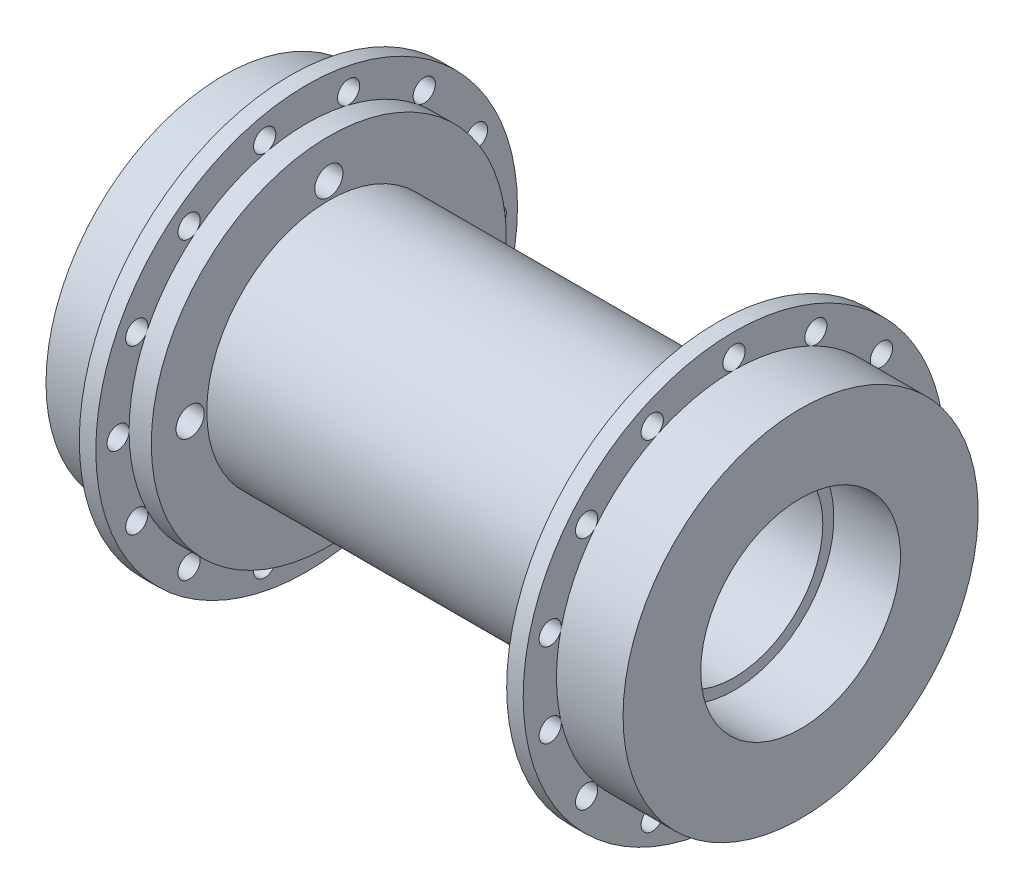
SolidWorks part; units mm, degrees
ref_plane "Front" through (0, 0, 0) normal (0, 0, 1) x (1, 0, 0)
ref_plane "Top" through (0, 0, 0) normal (0, 1, 0) x (1, 0, 0)
ref_plane "Right" through (0, 0, 0) normal (1, 0, 0) x (0, 0, -1)
sketch "Sketch1" plane through (0, 0, 0) normal (0, 0, 1) x (1, 0, 0)
  line L0 (-48.6984, 0) -> (52.2764, 0) construction
  line L1 (41.275, 25.4) -> (41.275, 14.2875)
  line L2 (41.275, 25.4) -> (31.75, 25.4)
  line L3 (31.75, 25.4) -> (31.75, 30.1625)
  line L4 (31.75, 30.1625) -> (29.3878, 30.1625)
  line L5 (29.3878, 30.1625) -> (29.3878, 25.4)
  line L6 (26.2128, 17.4625) -> (-26.2128, 17.4625)
  line L7 (0, 0) -> (0, 32.5655) construction
  line L8 (41.275, 14.2875) -> (31.75, 14.2875)
  line L9 (31.75, 14.2875) -> (31.75, 12.7)
  line L10 (31.75, 12.7) -> (-31.75, 12.7)
  line L11 (-29.3878, 30.1625) -> (-29.3878, 25.4)
  line L12 (-31.75, 30.1625) -> (-29.3878, 30.1625)
  line L13 (-31.75, 25.4) -> (-31.75, 30.1625)
  line L14 (-41.275, 25.4) -> (-31.75, 25.4)
  line L15 (-41.275, 25.4) -> (-41.275, 14.2875)
  line L16 (-41.275, 14.2875) -> (-31.75, 14.2875)
  line L17 (-31.75, 14.2875) -> (-31.75, 12.7)
  line L18 (26.2128, 25.4) -> (26.2128, 17.4625)
  line L19 (29.3878, 25.4) -> (26.2128, 25.4)
  line L20 (-29.3878, 25.4) -> (-26.2128, 25.4)
  line L21 (-26.2128, 25.4) -> (-26.2128, 17.4625)
  point P14 (0, 17.4625)
  point P23 (0, 12.7)
  dimension "D1" = 63.5
  dimension "D2" = 2.3622
  dimension "D3" = 60.325
  dimension "D4" = 25.4
  dimension "D5" = 28.575
  dimension "D6" = 9.525
  dimension "D7" = 9.525
  dimension "D8" = 50.8
  dimension "D9" = 34.925
  dimension "D10" = 3.175
revolve "Revolve1" add sketch "Sketch1" angle 360 about L0
hole_wizard "#10-32 Tapped Hole1" positions "Sketch3" profile "Sketch2" tap size "#10-32" standard "Ansi Inch"
sketch "Sketch3" plane through (-41.275, 0, 0) normal (-1, 0, 0) x (0, 0, 1)
  point P0 (19.8438, 0)
  point P1 (0, 19.8438)
  point P2 (-19.8438, 0)
  point P4 (0, -19.8438)
cosmetic thread "Cosmetic Thread1" parameters "D2"=4.826
cosmetic thread "Cosmetic Thread2" parameters "D2"=4.826
cosmetic thread "Cosmetic Thread3" parameters "D2"=4.826
cosmetic thread "Cosmetic Thread4" parameters "D2"=4.826
sketch "Sketch2" plane through (-41.275, 0, 19.8438) normal (0, 1, 0) x (0, 0, 1)
  line L0 (0, 0) -> (0, 15.0622)
  line L1 (0, 15.0622) -> (2.0193, 15.0622)
  line L2 (2.0193, 15.0622) -> (2.0193, 0)
  line L5 (2.0193, 0) -> (0, 0)
  line L11 (0, -6.35) -> (0, 107.95) construction
  dimension "Thru Tap Drill Dia." = 4.0386
  dimension "Thru Tap Drill Depth" = 15.0622
hole_wizard "1/8 (0.125000) Diameter Hole1" positions "Sketch5" profile "Sketch4" hole size "1/8" standard "Ansi Inch"
sketch "Sketch5" plane through (31.75, 0, 0) normal (1, 0, 0) x (0, 0, -1)
  line L0 (0, 0) -> (0, 26.9748) construction
  line L1 (0, 0) -> (0, -26.9748) construction
  point P0 (0, 26.9748)
  point P4 (11.7039, 24.3035)
  point P5 (21.0897, 16.8185)
  point P6 (26.2985, 6.0025)
  point P7 (26.2985, -6.0025)
  point P8 (21.0897, -16.8185)
  point P9 (11.7039, -24.3035)
  point P10 (0, -26.9748)
  point P11 (-11.7039, -24.3035)
  point P12 (-21.0897, -16.8185)
  point P13 (-26.2985, -6.0025)
  point P14 (-26.2985, 6.0025)
  point P15 (-21.0897, 16.8185)
  point P16 (-11.7039, 24.3035)
  point P17 (11.7039, 24.3035)
  point P18 (21.0897, 16.8185)
  point P19 (26.2985, 6.0025)
  point P24 (0, 26.9748)
  dimension "D1" = 26.9748
sketch "Sketch4" plane through (31.75, 26.9748, 0) normal (0, 1, 0) x (0, 0, -1)
  line L0 (0, 0) -> (0, 2.3622)
  line L1 (0, 2.3622) -> (1.5875, 2.3622)
  line L2 (1.5875, 2.3622) -> (1.5875, 0)
  line L5 (1.5875, 0) -> (0, 0)
  line L11 (0, -6.35) -> (0, 107.95) construction
  dimension "Thru Hole Dia." = 3.175
  dimension "Thru Hole Depth" = 2.3622
hole_wizard "1/8 (0.125000) Diameter Hole2" positions "Sketch7" profile "Sketch6" hole size "1/8" standard "Ansi Inch"
sketch "Sketch7" plane through (-31.75, 0, 0) normal (-1, 0, 0) x (0, 0, 1)
  line L0 (0, 0) -> (-26.9748, 0) construction
  line L1 (0, 0) -> (26.9748, 0) construction
  point P0 (-26.9748, 0)
  point P4 (-24.3035, 11.7039)
  point P5 (-16.8185, 21.0897)
  point P6 (-6.0025, 26.2985)
  point P7 (6.0025, 26.2985)
  point P8 (16.8185, 21.0897)
  point P9 (24.3035, 11.7039)
  point P10 (26.9748, 0)
  point P11 (24.3035, -11.7039)
  point P12 (16.8185, -21.0897)
  point P13 (6.0025, -26.2985)
  point P14 (-6.0025, -26.2985)
  point P15 (-16.8185, -21.0897)
  point P16 (-24.3035, -11.7039)
  point P17 (-24.3035, 11.7039)
  point P18 (-16.8185, 21.0897)
  point P20 (-6.0025, 26.2985)
  point P24 (-26.9748, 0)
  dimension "D1" = 26.9748
sketch "Sketch6" plane through (-31.75, 0, -26.9748) normal (0, 1, 0) x (0, 0, 1)
  line L0 (0, 0) -> (0, 2.3622)
  line L1 (0, 2.3622) -> (1.5875, 2.3622)
  line L2 (1.5875, 2.3622) -> (1.5875, 0)
  line L5 (1.5875, 0) -> (0, 0)
  line L11 (0, -6.35) -> (0, 107.95) construction
  dimension "Thru Hole Dia." = 3.175
  dimension "Thru Hole Depth" = 2.3622
